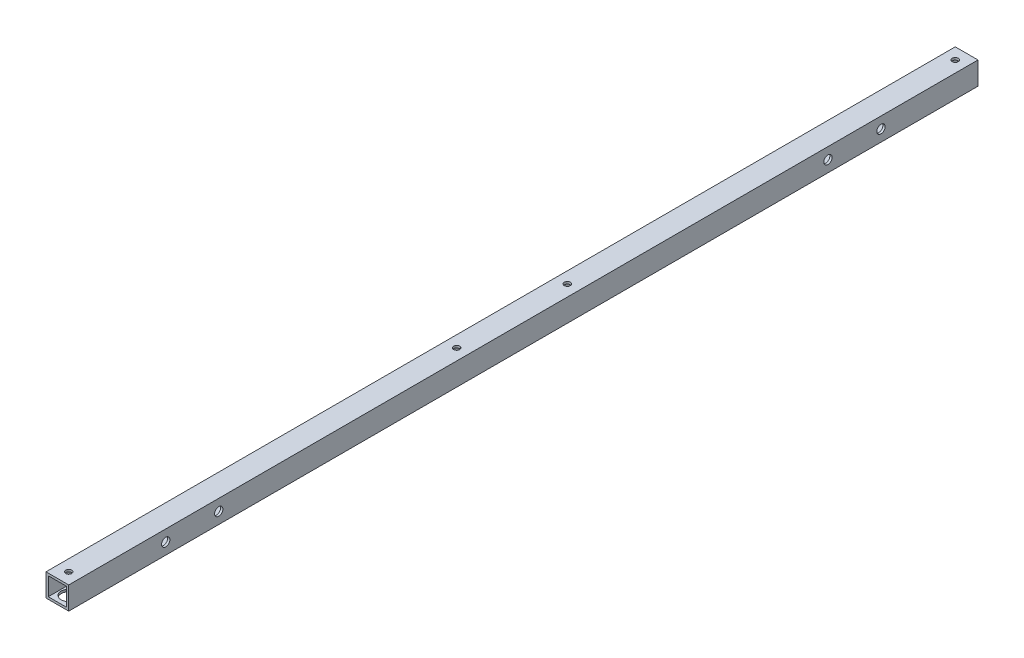
SolidWorks part; units mm, degrees
material "6063-T5"
ref_plane "正面" through (0, 0, 0) normal (0, 0, 1) x (1, 0, 0)
ref_plane "平面" through (0, 0, 0) normal (0, 1, 0) x (1, 0, 0)
ref_plane "右側面" through (0, 0, 0) normal (1, 0, 0) x (0, 0, -1)
sketch "ｽｹｯﾁ1" plane through (0, 0, 0) normal (0, 0, 1) x (1, 0, 0)
  line L1 (-7.5, -7.5) -> (7.5, -7.5)
  line L2 (-7.5, -7.5) -> (-7.5, 7.5)
  line L3 (-7.5, 7.5) -> (7.5, 7.5)
  line L4 (7.5, -7.5) -> (7.5, 7.5)
  line L5 (-7.5, -7.5) -> (7.5, 7.5) construction
  line L6 (-7.5, 7.5) -> (7.5, -7.5) construction
  line L7 (-6, -6) -> (6, -6)
  line L8 (-6, -6) -> (-6, 6)
  line L9 (-6, 6) -> (6, 6)
  line L10 (6, -6) -> (6, 6)
  line L11 (-6, -6) -> (6, 6) construction
  line L12 (-6, 6) -> (6, -6) construction
  point P0 (0, 0)
  point P6 (0, 0)
  dimension "D1" = 1.5
  dimension "D2" = 15
  dimension "D3" = 15
extrude "ﾎﾞｽ - 押し出し1" add sketch "ｽｹｯﾁ1" along normal blind 600
sketch "ｽｹｯﾁ3" plane through (0, 7.5, 0) normal (0, 1, 0) x (1, 0, 0)
  line L2 (7.5, -600) -> (7.5, 0) construction
  line L3 (7.5, 0) -> (-7.5, 0) construction
  circle A1 centre (0, -7.5) radius 2
  circle A6 centre (0, -592.5) radius 2
  dimension "D2" = 7.5
  dimension "D3" = 4
  dimension "D9" = 7.5
  dimension "D11" = 7.5
  dimension "D4" = 7.5
  dimension "D5" = 4
extrude "ｶｯﾄ - 押し出し2" cut sketch "ｽｹｯﾁ3" against normal blind 25
sketch "ｽｹｯﾁ4" plane through (7.5, 0, 0) normal (1, 0, 0) x (0, 0, -1)
  line L0 (-600, -7.5) -> (-600, 7.5) construction
  line L1 (-600, -7.5) -> (0, -7.5) construction
  line L2 (0, -7.5) -> (0, 7.5) construction
  circle A0 centre (-536, 0) radius 2.75
  circle A1 centre (-501, 0) radius 2.75
  circle A2 centre (-99, 0) radius 2.75
  circle A3 centre (-64, 0) radius 2.75
  dimension "D2" = 7.5
  dimension "D3" = 5.5
  dimension "D5" = 35
  dimension "D7" = 64
  dimension "D1" = 64
  dimension "D4" = 2
  dimension "D6" = 2
extrude "ｶｯﾄ - 押し出し3" cut sketch "ｽｹｯﾁ4" against normal blind 20
sketch "ｽｹｯﾁ6" plane through (0, 7.5, 0) normal (0, 1, 0) x (1, 0, 0)
  line L0 (-7.5, -600) -> (-7.5, 0) construction
  line L1 (7.5, -600) -> (7.5, 0) construction
  circle A0 centre (0, -336.5) radius 2
  circle A1 centre (0, -263.5) radius 2
  point P6 (-7.5, -300)
  dimension "D2" = 73
  dimension "D3" = 7.5
  dimension "D4" = 7.5
  dimension "D5" = 4
  dimension "D6" = 4
  dimension "D1" = 36.5
extrude "ｶｯﾄ - 押し出し4" cut sketch "ｽｹｯﾁ6" against normal blind 20
sketch "ｽｹｯﾁ9" plane through (0, -7.5, 0) normal (0, -1, 0) x (1, 0, 0)
  circle A0 centre (0, 592.5) radius 5
  circle A1 centre (0, 336.5) radius 5
  circle A2 centre (0, 263.5) radius 5
  circle A3 centre (0, 7.5) radius 5
  dimension "D1" = 10
  dimension "D2" = 10
  dimension "D3" = 10
  dimension "D4" = 10
extrude "ｶｯﾄ - 押し出し7" cut sketch "ｽｹｯﾁ9" against normal blind 10
